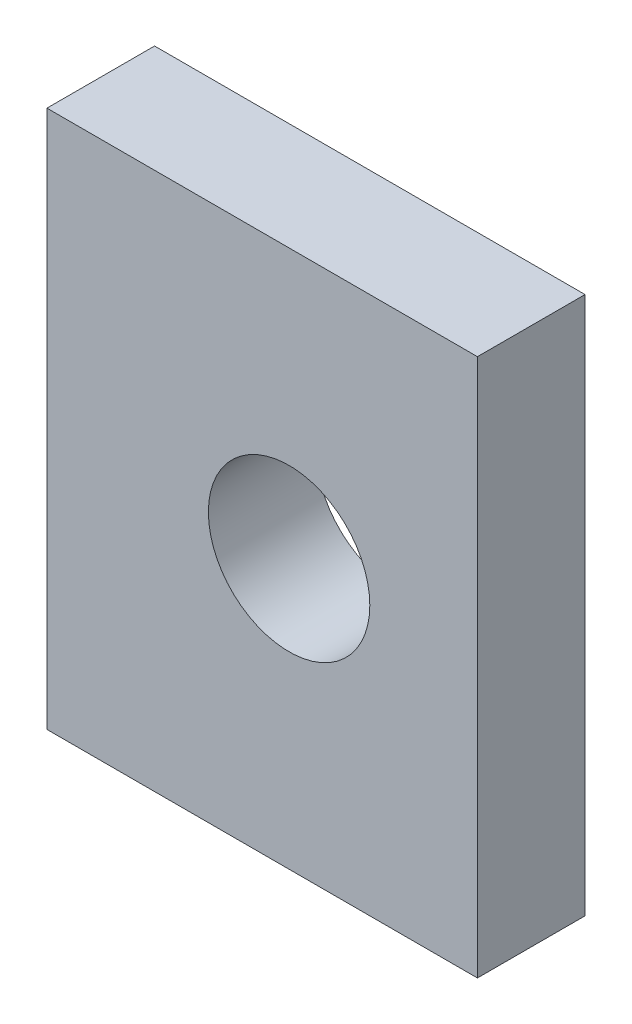
SolidWorks part; units mm, degrees
ref_plane "Front Plane" through (0, 0, 0) normal (0, 0, 1) x (1, 0, 0)
ref_plane "Top Plane" through (0, 0, 0) normal (0, 1, 0) x (1, 0, 0)
ref_plane "Right Plane" through (0, 0, 0) normal (1, 0, 0) x (0, 0, -1)
sketch "Sketch1" plane through (0, 0, 0) normal (0, 0, 1) x (1, 0, 0)
  line L0 (0, 10) -> (8, 10)
  line L1 (8, 0) -> (0, 0)
  line L2 (0, 10) -> (0, 0)
  line L3 (8, 10) -> (8, 0)
  circle A0 centre (4.5, 5) radius 1.5
  dimension "D3" = 8
  dimension "D1" = 3
  dimension "D2" = 4.5
  dimension "D4" = 5
  dimension "D5" = 10
extrude "Boss-Extrude1" add sketch "Sketch1" along normal blind 2
